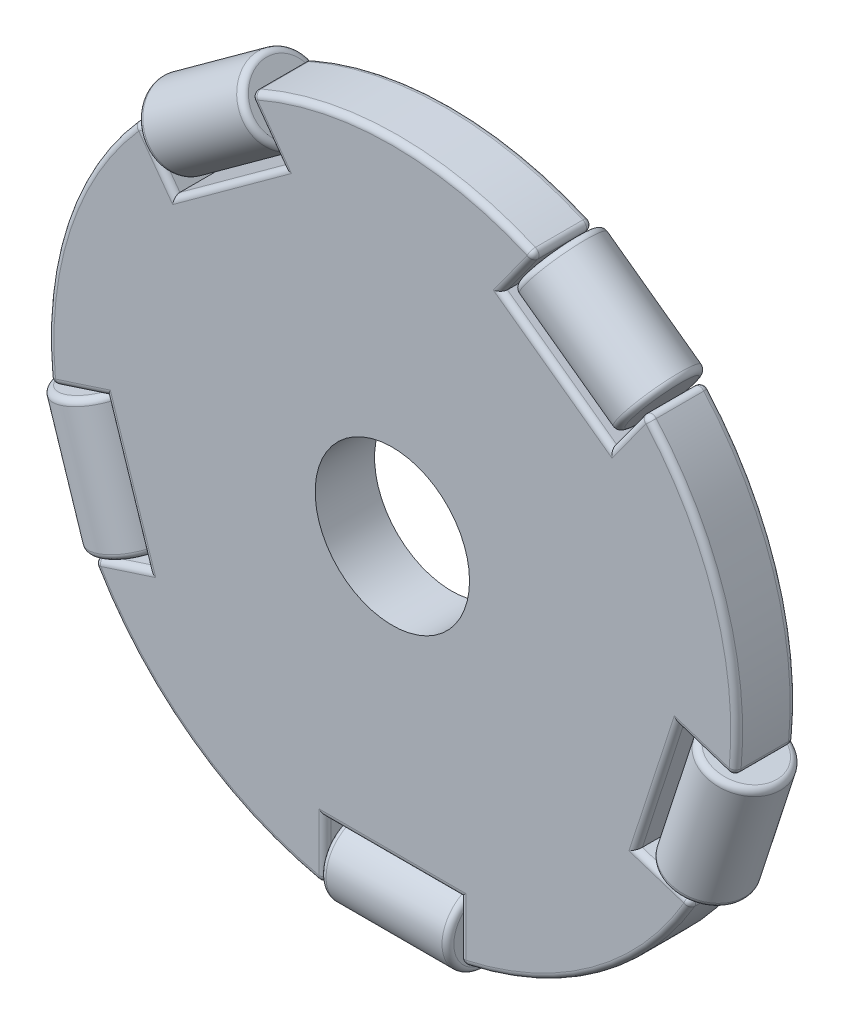
SolidWorks part; units mm, degrees
ref_plane "Front Plane" through (0, 0, 0) normal (0, 0, 1) x (1, 0, 0)
ref_plane "Top Plane" through (0, 0, 0) normal (0, 1, 0) x (1, 0, 0)
ref_plane "Right Plane" through (0, 0, 0) normal (1, 0, 0) x (0, 0, -1)
sketch "Sketch1" plane through (0, 0, 0) normal (0, 0, 1) x (1, 0, 0)
  line L0 (0, 0) -> (0, 29) construction
  line L1 (0, 0) -> (27.5806, 8.9615) construction
  line L2 (0, 0) -> (17.0458, -23.4615) construction
  line L3 (0, 0) -> (-17.0458, -23.4615) construction
  line L4 (0, 0) -> (-27.5806, 8.9615) construction
  line L5 (-9.1935, 22.3205) -> (-18.3871, 15.641)
  line L6 (-20.5574, -12.6538) -> (-24.069, -1.8462)
  line L7 (-5.6819, -23.4615) -> (5.6819, -23.4615)
  line L8 (20.5574, -12.6538) -> (24.069, -1.8462)
  line L9 (9.1935, 22.3205) -> (18.3871, 15.641)
  line L10 (-18.3871, 15.641) -> (-21.3122, 19.667)
  line L11 (-9.1935, 22.3205) -> (-12.1186, 26.3465)
  line L12 (9.1935, 22.3205) -> (12.1186, 26.3465)
  line L13 (18.3871, 15.641) -> (21.3122, 19.667)
  line L14 (-24.069, -1.8462) -> (-28.8019, -3.384)
  line L15 (-20.5574, -12.6538) -> (-25.2903, -14.1916)
  line L16 (24.069, -1.8462) -> (28.8019, -3.384)
  line L17 (20.5574, -12.6538) -> (25.2903, -14.1916)
  line L18 (-5.6819, -23.4615) -> (-5.6819, -28.4379)
  line L19 (5.6819, -23.4615) -> (5.6819, -28.4379)
  arc A0 (-21.3122, 19.667) -> (-28.8019, -3.384) centre (0, 0) ccw
  arc A1 (12.1186, 26.3465) -> (-12.1186, 26.3465) centre (0, 0) ccw
  arc A2 (28.8019, -3.384) -> (21.3122, 19.667) centre (0, 0) ccw
  arc A3 (5.6819, -28.4379) -> (25.2903, -14.1916) centre (0, 0) ccw
  arc A4 (-25.2903, -14.1916) -> (-5.6819, -28.4379) centre (0, 0) ccw
  point P3 (-9.1935, 22.3205)
  point P9 (-18.3871, 15.641)
  dimension "D1" = 58
  dimension "D2" = 72
  dimension "D3" = 72
  dimension "D4" = 72
  dimension "D5" = 72
  dimension "D6" = 11.3638
  dimension "D7" = 11.3638
extrude "Boss-Extrude1" add sketch "Sketch1" along normal mid plane 5
sketch "Sketch2" plane through (0, 0, 0) normal (0, 0, 1) x (1, 0, 0)
  line L0 (-20.2016, 18.6489) -> (-11.4935, 24.9757)
  line L1 (-18.3871, 15.641) -> (-21.3122, 19.667) construction
  line L2 (-12.1186, 26.3465) -> (-9.1935, 22.3205) construction
  line L3 (-9.1935, 22.3205) -> (-18.3871, 15.641) construction
  line L4 (-20.2016, 18.6489) -> (-18.3207, 16.06)
  line L5 (-18.3207, 16.06) -> (-9.6126, 22.3869)
  line L6 (-9.6126, 22.3869) -> (-11.4935, 24.9757)
  dimension "D1" = 3.5
  dimension "D2" = 0.3
  dimension "D3" = 0.3
  dimension "D4" = 0.3
revolve "Revolve1" add sketch "Sketch2" angle 360 about L0
sketch "Sketch8" plane through (0, 0, 0) normal (0, 0, 1) x (1, 0, 0)
  line L0 (-27.305, -3.213) -> (-23.9788, -13.4501)
  line L1 (-28.8019, -3.384) -> (-24.069, -1.8462) construction
  line L2 (-20.5574, -12.6538) -> (-25.2903, -14.1916) construction
  line L3 (-23.9788, -13.4501) -> (-20.9354, -12.4612)
  line L4 (-20.9354, -12.4612) -> (-24.2616, -2.2242)
  line L5 (-24.2616, -2.2242) -> (-27.305, -3.213)
  line L6 (-24.069, -1.8462) -> (-20.5574, -12.6538) construction
  dimension "D1" = 0.3
  dimension "D2" = 0.3
  dimension "D3" = 0.3
  dimension "D4" = 3.5
revolve "Revolve2" add sketch "Sketch8" angle 360 about L0
sketch "Sketch9" plane through (0, 0, 0) normal (0, 0, 1) x (1, 0, 0)
  line L0 (-5.3819, -26.9615) -> (5.3819, -26.9615)
  line L1 (-5.6819, -28.4379) -> (-5.6819, -23.4615) construction
  line L2 (5.6819, -23.4615) -> (5.6819, -28.4379) construction
  line L3 (5.3819, -26.9615) -> (5.3819, -23.7615)
  line L4 (5.3819, -23.7615) -> (-5.3819, -23.7615)
  line L5 (-5.3819, -23.7615) -> (-5.3819, -26.9615)
  line L6 (-5.6819, -23.4615) -> (5.6819, -23.4615) construction
  dimension "D1" = 3.5
  dimension "D2" = 0.3
  dimension "D3" = 0.3
  dimension "D4" = 0.3
revolve "Revolve3" add sketch "Sketch9" angle 360 about L0
sketch "Sketch10" plane through (0, 0, 0) normal (0, 0, 1) x (1, 0, 0)
  line L0 (23.9788, -13.4501) -> (27.305, -3.213)
  line L1 (25.2903, -14.1916) -> (20.5574, -12.6538) construction
  line L2 (24.069, -1.8462) -> (28.8019, -3.384) construction
  line L3 (27.305, -3.213) -> (24.2616, -2.2242)
  line L4 (24.2616, -2.2242) -> (20.9354, -12.4612)
  line L5 (20.9354, -12.4612) -> (23.9788, -13.4501)
  line L6 (20.5574, -12.6538) -> (24.069, -1.8462) construction
  dimension "D1" = 3.5
  dimension "D2" = 0.3
  dimension "D3" = 0.3
  dimension "D4" = 0.3
revolve "Revolve4" add sketch "Sketch10" angle 360 about L0
sketch "Sketch11" plane through (0, 0, 0) normal (0, 0, 1) x (1, 0, 0)
  line L0 (20.2016, 18.6489) -> (11.4935, 24.9757)
  line L1 (21.3122, 19.667) -> (18.3871, 15.641) construction
  line L2 (9.1935, 22.3205) -> (12.1186, 26.3465) construction
  line L3 (20.2016, 18.6489) -> (18.3207, 16.06)
  line L4 (18.3207, 16.06) -> (9.6126, 22.3869)
  line L5 (9.6126, 22.3869) -> (11.4935, 24.9757)
  line L6 (18.3871, 15.641) -> (9.1935, 22.3205) construction
  dimension "D1" = 3.5
  dimension "D2" = 0.3
  dimension "D3" = 0.3
  dimension "D4" = 0.3
revolve "Revolve5" add sketch "Sketch11" angle 360 about L0
fillet "Fillet1" radius 0.5 50 edges at (-26.4355, -2.6151, -2.5) (-22.3132, -7.25, -2.5) (-22.9238, -13.4227, -2.5) (-5.6819, -25.9497, -2.5) (0, -23.4615, -2.5) (5.6819, -25.9497, -2.5) (22.9238, -13.4227, -2.5) (22.3132, -7.25, -2.5) (26.4355, -2.6151, -2.5) (19.8496, 17.654, -2.5) (13.7903, 18.9807, -2.5) (10.6561, 24.3335, -2.5) (-10.6561, 24.3335, -2.5) (-13.7903, 18.9807, -2.5) (-19.8496, 17.654, -2.5) (-25.2903, -14.1916, 0) (-5.6819, -28.4379, 0) (-17.0458, -23.4615, -2.5) (5.6819, -28.4379, 0) (25.2903, -14.1916, 0) (17.0458, -23.4615, -2.5) (28.8019, -3.384, 0) (21.3122, 19.667, 0) (27.5806, 8.9615, -2.5) (-21.3122, 19.667, 0) (-28.8019, -3.384, 0) (-27.5806, 8.9615, -2.5) (12.1186, 26.3465, 0) (-12.1186, 26.3465, 0) (0, 29, -2.5) (-13.7903, 18.9807, 2.5) (-10.6561, 24.3335, 2.5) (0, 29, 2.5) (10.6561, 24.3335, 2.5) (13.7903, 18.9807, 2.5) (19.8496, 17.654, 2.5) (27.5806, 8.9615, 2.5) (26.4355, -2.6151, 2.5) (22.3132, -7.25, 2.5) (22.9238, -13.4227, 2.5) (17.0458, -23.4615, 2.5) (5.6819, -25.9497, 2.5) (0, -23.4615, 2.5) (-5.6819, -25.9497, 2.5) (-17.0458, -23.4615, 2.5) (-22.9238, -13.4227, 2.5) (-22.3132, -7.25, 2.5) (-26.4355, -2.6151, 2.5) (-27.5806, 8.9615, 2.5) (-19.8496, 17.654, 2.5)
fillet "Fillet2" radius 0.5 2 edges at (5.3819, -26.9615, 3.2) (-5.3819, -26.9615, 3.2)
fillet "Fillet3" radius 0.5 2 edges at (30.3484, -4.2019, 0) (27.0222, -14.4389, 0)
fillet "Fillet4" radius 0.5 2 edges at (22.0825, 21.2377, 0) (13.3744, 27.5646, 0)
fillet "Fillet5" radius 0.5 2 edges at (-18.3207, 16.06, 0) (-9.6126, 22.3869, 0)
fillet "Fillet6" radius 0.5 2 edges at (-30.3484, -4.2019, 0) (-27.0222, -14.4389, 0)
sketch "Sketch12" plane through (0, 0, 0) normal (0, 0, 1) x (1, 0, 0)
  circle A0 centre (0, 0) radius 6.5
  dimension "D1" = 13
extrude "Cut-Extrude1" cut sketch "Sketch12" along normal mid plane 5
